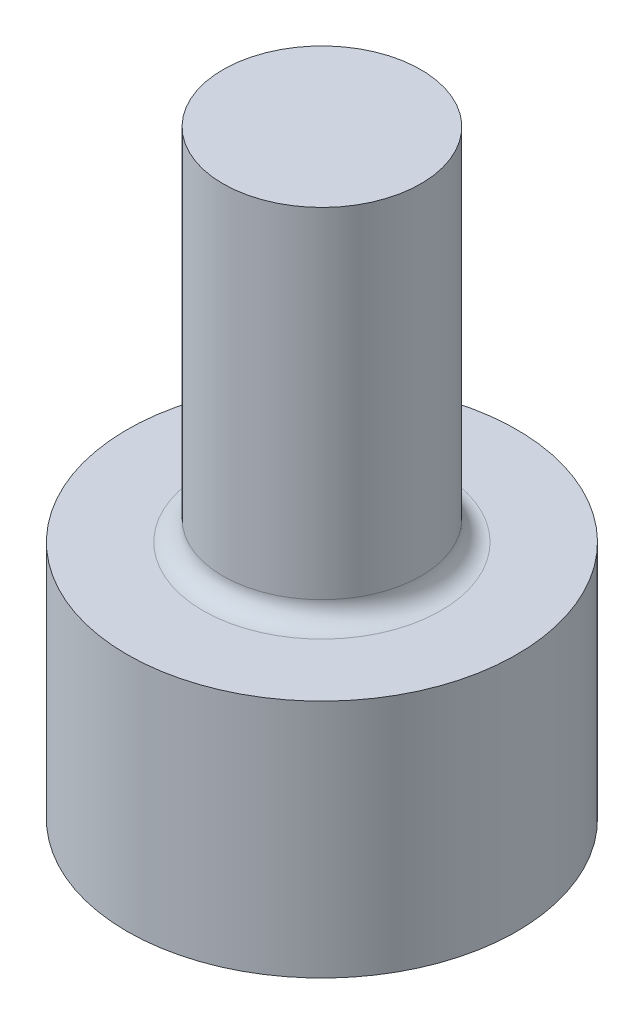
SolidWorks part; units mm, degrees
ref_plane "Front Plane" through (0, 0, 0) normal (0, 0, 1) x (1, 0, 0)
ref_plane "Top Plane" through (0, 0, 0) normal (0, 1, 0) x (1, 0, 0)
ref_plane "Right Plane" through (0, 0, 0) normal (1, 0, 0) x (0, 0, -1)
sketch "Sketch1" plane through (0, 0, 0) normal (0, 1, 0) x (1, 0, 0)
  circle A0 centre (0, 0) radius 1.875
  circle A1 centre (0, 0) radius 4.875
  dimension "D1" = 3.75
  dimension "D2" = 3
extrude "Boss-Extrude1" add sketch "Sketch1" along normal blind 6
sketch "Sketch2" plane through (0, 6, 0) normal (0, 1, 0) x (1, 0, 0)
  circle A0 centre (0, 0) radius 2.475
  dimension "D1" = 4.95
extrude "Boss-Extrude2" add sketch "Sketch2" along normal blind 9
fillet "Fillet1" radius 0.5 1 edges at (0, 6, 2.475)
